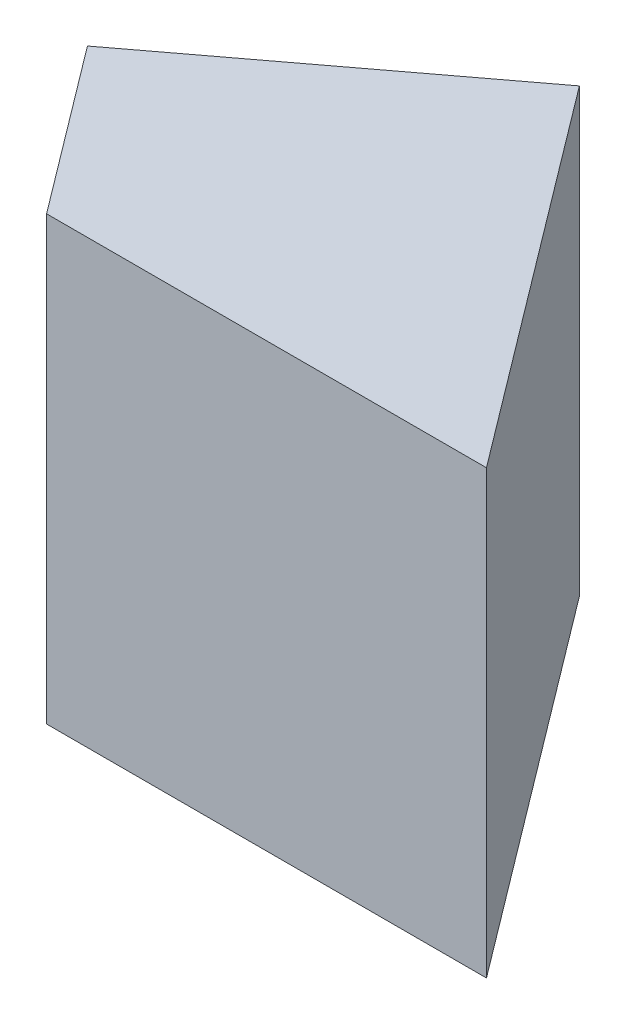
SolidWorks part; units mm, degrees
material "Стекло"
ref_plane "Спереди" through (0, 0, 0) normal (0, 0, 1) x (1, 0, 0)
ref_plane "Сверху" through (0, 0, 0) normal (0, 1, 0) x (1, 0, 0)
ref_plane "Справа" through (0, 0, 0) normal (1, 0, 0) x (0, 0, -1)
ref_plane "Плоскость1" through (0, -10, 0) normal (0, 1, 0) x (-1, 0, 0)
sketch "Эскиз1" plane through (0, -10, 0) normal (0, 1, 0) x (1, 0, 0)
  line L0 (-10.9277, 0) -> (1.7706, 9.5689)
  line L1 (1.7706, 9.5689) -> (14.6338, -7.5011)
  line L2 (14.6338, -7.5011) -> (-5.2752, -7.5011)
  line L3 (-5.2752, -7.5011) -> (-10.9277, 0)
  dimension "D1" = 53
  dimension "D2" = 15.9
  dimension "D3" = 17.07
extrude "Бобышка-Вытянуть1" add sketch "Эскиз1" along normal blind 20
sketch "Эскиз2" plane through (0, 0, 0) normal (0, 0, 1) x (1, 0, 0)
  line L0 (-10.9277, 10) -> (8.9813, 10)
  line L1 (8.9813, 10) -> (8.9813, -10)
  line L2 (8.9813, -10) -> (-10.9277, -10)
  line L3 (-10.9277, -10) -> (-10.9277, 10)
